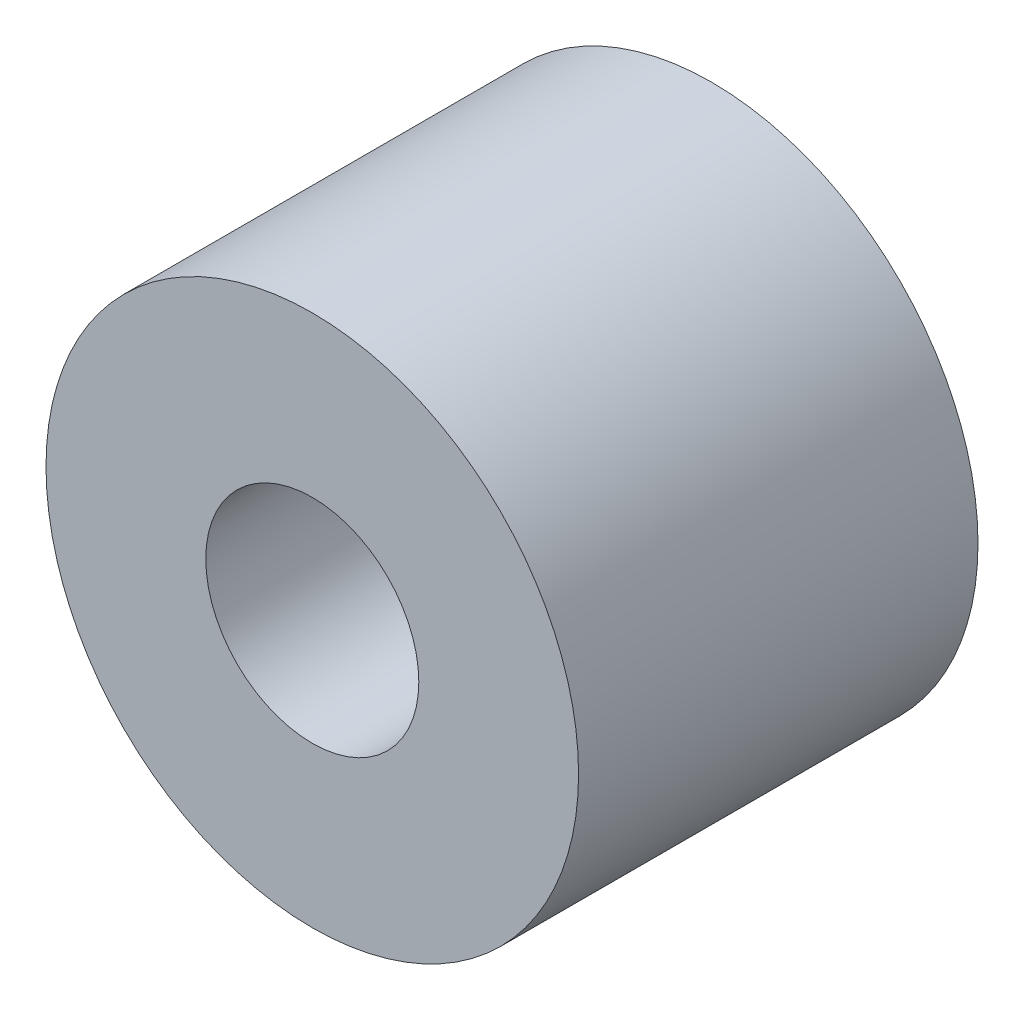
SolidWorks part; units mm, degrees
ref_plane "前视基准面" through (0, 0, 0) normal (0, 0, 1) x (1, 0, 0)
ref_plane "上视基准面" through (0, 0, 0) normal (0, 1, 0) x (1, 0, 0)
ref_plane "右视基准面" through (0, 0, 0) normal (1, 0, 0) x (0, 0, -1)
sketch "草图1" plane through (0, 0, 0) normal (0, 0, 1) x (1, 0, 0)
  circle A0 centre (0, 0) radius 10
  circle A1 centre (0, 0) radius 4
  dimension "D1" = 20
  dimension "D2" = 8
extrude "凸台-拉伸1" add sketch "草图1" along normal blind 15
